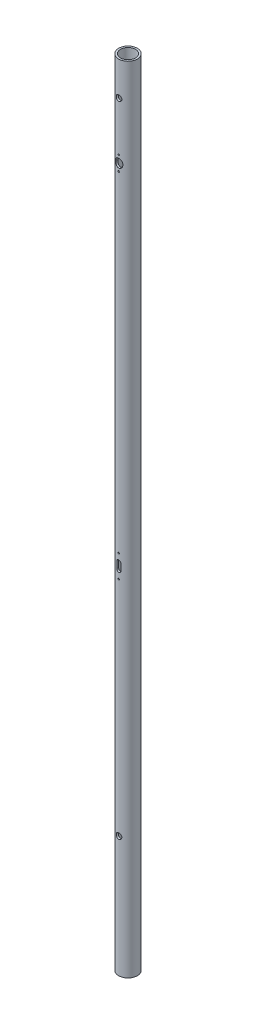
SolidWorks part; units mm, degrees
ref_plane "Front Plane" through (0, 0, 0) normal (0, 0, 1) x (1, 0, 0)
ref_plane "Top Plane" through (0, 0, 0) normal (0, 1, 0) x (1, 0, 0)
ref_plane "Right Plane" through (0, 0, 0) normal (1, 0, 0) x (0, 0, -1)
sketch "Sketch1" plane through (0, 0, 0) normal (0, 1, 0) x (1, 0, 0)
  circle A0 centre (0, 0) radius 21.082
  circle A1 centre (0, 0) radius 16.891
  dimension "D1" = 42.164
  dimension "D2" = 33.782
extrude "Boss-Extrude1" add sketch "Sketch1" along normal blind 1790.7
sketch "Sketch2" plane through (0, 0, 0) normal (0, 0, 1) x (1, 0, 0)
  line L0 (21.082, 1790.7) -> (-21.082, 1790.7) construction
  line L1 (21.082, 1790.7) -> (-21.082, 1790.7) construction
  line L2 (0, 1790.7) -> (0, 0) construction
  line L3 (-21.082, 0) -> (21.082, 0) construction
  circle A0 centre (0, 1714.5) radius 6.35
  circle A1 centre (0, 273.05) radius 6.35
  dimension "D1" = 12.7
  dimension "D3" = 12.7
  dimension "D2" = 76.2
  dimension "D4" = 273.05
extrude "Cut-Extrude1" cut sketch "Sketch2" along normal mid plane 42.164
sketch "Sketch3" plane through (0, 0, 0) normal (0, 0, 1) x (1, 0, 0)
  line L0 (21.082, 1790.7) -> (-21.082, 1790.7) construction
  line L1 (21.082, 1790.7) -> (-21.082, 1790.7) construction
  line L2 (0, 1790.7) -> (0, 0) construction
  circle A0 centre (0, 1603.756) radius 1.651
  circle A1 centre (0, 1714.5) radius 6.35 construction
  circle A2 centre (0, 1570.99) radius 1.651
  circle A3 centre (0, 774.7) radius 1.651
  circle A4 centre (0, 273.05) radius 6.35 construction
  circle A5 centre (0, 825.5) radius 1.651
  dimension "D1" = 3.302
  dimension "D2" = 110.744
  dimension "D4" = 3.302
  dimension "D3" = 32.766
  dimension "D5" = 501.65
  dimension "D6" = 50.8
extrude "Cut-Extrude2" cut sketch "Sketch3" against normal mid plane 42.164
sketch "Sketch5" plane through (0, 0, 0) normal (0, 0, 1) x (1, 0, 0)
  line L0 (21.082, 1790.7) -> (-21.082, 1790.7) construction
  line L1 (21.082, 1790.7) -> (-21.082, 1790.7) construction
  line L2 (0, 1790.7) -> (0, 0) construction
  line L3 (0, 1589.024) -> (0, 1585.722) construction
  line L4 (7.874, 1589.024) -> (7.874, 1585.722)
  line L5 (-7.874, 1589.024) -> (-7.874, 1585.722)
  line L6 (0, 807.466) -> (0, 792.734) construction
  line L7 (4.826, 807.466) -> (4.826, 792.734)
  line L8 (-4.826, 807.466) -> (-4.826, 792.734)
  arc A0 (7.874, 1589.024) -> (-7.874, 1589.024) centre (0, 1589.024) ccw
  arc A1 (-7.874, 1585.722) -> (7.874, 1585.722) centre (0, 1585.722) ccw
  circle A3 centre (0, 1570.99) radius 1.651 construction
  circle A4 centre (0, 1603.756) radius 1.651 construction
  arc A5 (4.826, 807.466) -> (-4.826, 807.466) centre (0, 807.466) ccw
  arc A6 (-4.826, 792.734) -> (4.826, 792.734) centre (0, 792.734) ccw
  circle A7 centre (0, 774.7) radius 1.651 construction
  point P7 (0, 1587.373)
  point P18 (0, 800.1)
  dimension "D2" = 7.874
  dimension "D3" = 14.732
  dimension "D6" = 4.826
  dimension "D1" = 14.732
  dimension "D4" = 14.732
  dimension "D5" = 18.034
extrude "Cut-Extrude3" cut sketch "Sketch5" against normal mid plane 42.164
